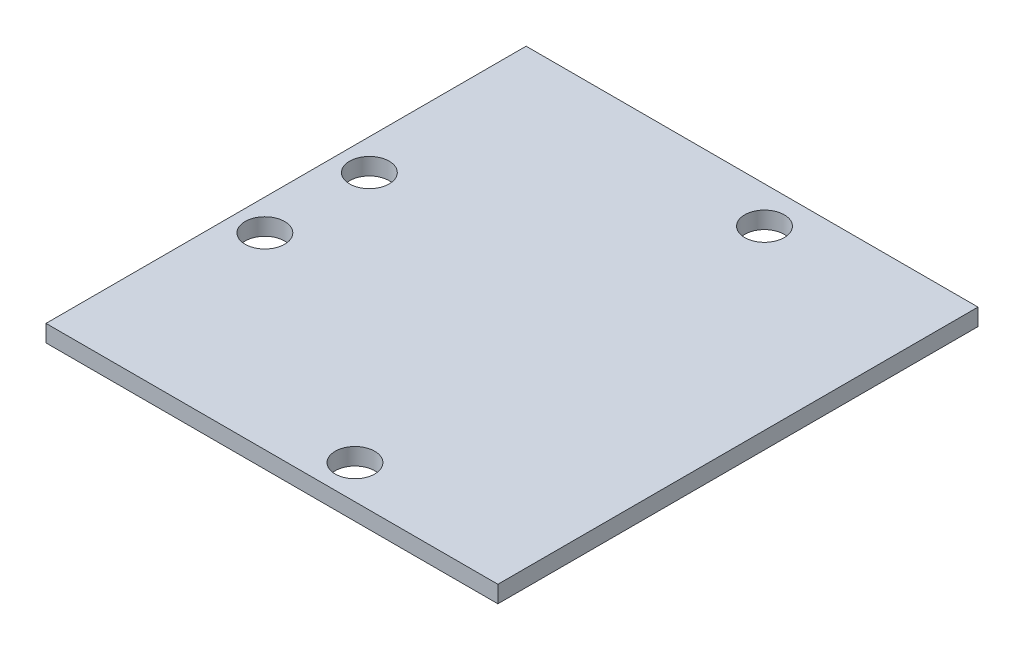
SolidWorks part; units mm, degrees
ref_plane "Front Plane" through (0, 0, 0) normal (0, 0, 1) x (1, 0, 0)
ref_plane "Top Plane" through (0, 0, 0) normal (0, 1, 0) x (1, 0, 0)
ref_plane "Right Plane" through (0, 0, 0) normal (1, 0, 0) x (0, 0, -1)
sketch "Sketch1" plane through (0, 0, 0) normal (0, 1, 0) x (1, 0, 0)
  line L1 (0, 0) -> (80, 0)
  line L2 (0, 0) -> (0, 85)
  line L3 (0, 85) -> (80, 85)
  line L4 (80, 0) -> (80, 85)
  dimension "D1" = 85
  dimension "D2" = 80
extrude "Boss-Extrude1" add sketch "Sketch1" along normal blind 3
sketch "Sketch2" plane through (0, 3, 0) normal (0, 1, 0) x (1, 0, 0)
  line L0 (0, 0) -> (80, 0) construction
  line L2 (0, 85) -> (0, 0) construction
  circle A0 centre (5.5, 33.25) radius 3.5
  circle A1 centre (5.5, 51.75) radius 3.5
  circle A2 centre (48.7, 78.5) radius 3.5
  circle A3 centre (48.7, 6) radius 3.5
  dimension "D1" = 7
  dimension "D2" = 7
  dimension "D4" = 7
  dimension "D6" = 7
  dimension "D7" = 6
  dimension "D10" = 43.2
  dimension "D8" = 48.7
  dimension "D3" = 18.5
  dimension "D5" = 72.5
  dimension "D9" = 33.25
extrude "Cut-Extrude1" cut sketch "Sketch2" against normal through all
sketch "Sketch3" plane through (0, 3, 0) normal (0, 1, 0) x (1, 0, 0)
  line L0 (0, 42.5) -> (80, 42.5) construction
  line L1 (0, 85) -> (0, 0) construction
  line L2 (80, 0) -> (80, 85) construction
sketch "Sketch4" plane through (0, 0, 0) normal (0, -1, 0) x (1, 0, 0)
  line L0 (0, -42.5) -> (80, -42.5) construction
  line L1 (0, -85) -> (0, 0) construction
